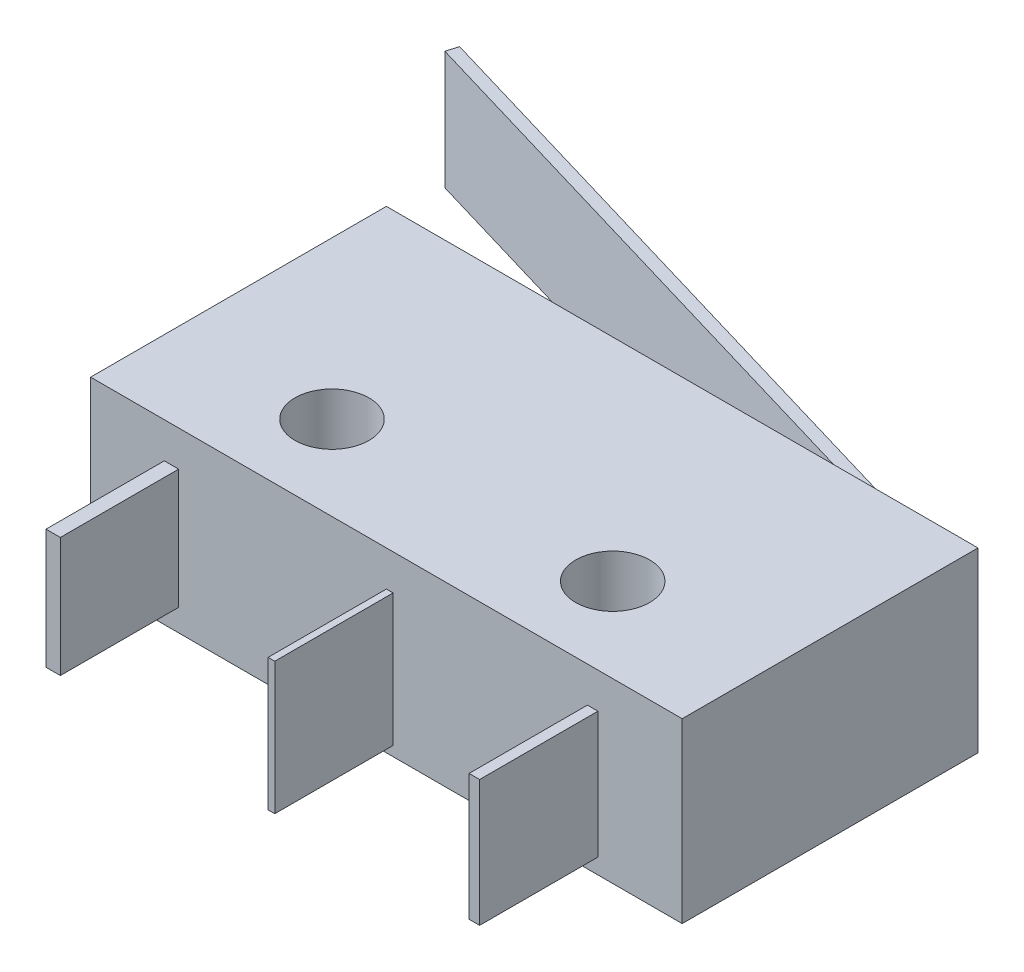
SolidWorks part; units mm, degrees
ref_plane "Plano frontal" through (0, 0, 0) normal (0, 0, 1) x (1, 0, 0)
ref_plane "Plano superior" through (0, 0, 0) normal (0, 1, 0) x (1, 0, 0)
ref_plane "Plano direito" through (0, 0, 0) normal (1, 0, 0) x (0, 0, -1)
sketch "Esboço1" plane through (0, 0, 0) normal (0, 1, 0) x (1, 0, 0)
  line L0 (-4.69, -2.15) -> (4.8, -2.15) construction
  line L1 (-10, 5) -> (10, 5)
  line L2 (-10, 5) -> (-10, -5)
  line L3 (-10, -5) -> (10, -5)
  line L4 (10, 5) -> (10, -5)
  line L5 (-10, 5) -> (10, -5) construction
  line L6 (-10, -5) -> (10, 5) construction
  circle A0 centre (-4.69, -2.15) radius 1.25
  circle A1 centre (4.8, -2.15) radius 1.25
  point P0 (0, 0)
  dimension "D3" = 5.31
  dimension "D4" = 2.85
  dimension "D5" = 2.5
  dimension "D6" = 5.2
  dimension "D7" = 2.5
  dimension "D1" = 20
  dimension "D2" = 10
extrude "Ressalto-extrusão1" add sketch "Esboço1" along normal blind 6
sketch "Esboço2" plane through (0, 0, 5) normal (0, 0, 1) x (1, 0, 0)
  line L1 (-7.5075, 4.796) -> (-7.0221, 4.796)
  line L2 (-7.5075, 4.796) -> (-7.5075, 0.751)
  line L3 (-7.5075, 0.751) -> (-7.0221, 0.751)
  line L4 (-7.0221, 4.796) -> (-7.0221, 0.751)
  line L5 (0, 4.796) -> (0.2265, 4.796)
  line L6 (0, 4.796) -> (0, 0.3303)
  line L7 (0, 0.3303) -> (0.2265, 0.3303)
  line L8 (0.2265, 4.796) -> (0.2265, 0.3303)
  line L9 (6.7956, 4.796) -> (7.1515, 4.796)
  line L10 (6.7956, 4.796) -> (6.7956, 0.5245)
  line L11 (6.7956, 0.5245) -> (7.1515, 0.5245)
  line L12 (7.1515, 4.796) -> (7.1515, 0.5245)
extrude "Ressalto-extrusão2" add sketch "Esboço2" along normal blind 4
sketch "Esboço3" plane through (0, 6, 0) normal (0, 1, 0) x (1, 0, 0)
  line L0 (7.5, 5) -> (-14.5534, 11.5304)
  line L1 (10, 5) -> (-10, 5) construction
  line L2 (10, -5) -> (10, 5) construction
  dimension "D1" = 23
  dimension "D2" = 2.5
extrude "Extrusão-Fina1" add sketch "Esboço3" against normal blind 4 from offset 1 separate body thin
